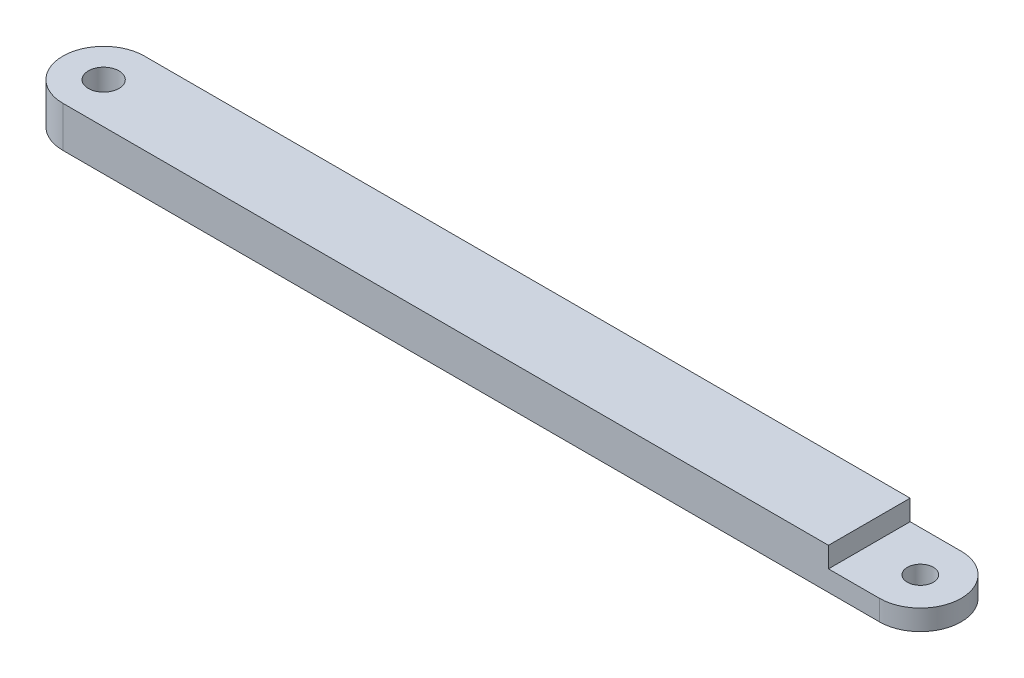
SolidWorks part; units mm, degrees
ref_plane "Front" through (0, 0, 0) normal (0, 0, 1) x (1, 0, 0)
ref_plane "Top" through (0, 0, 0) normal (0, 1, 0) x (1, 0, 0)
ref_plane "Right" through (0, 0, 0) normal (1, 0, 0) x (0, 0, -1)
sketch "Sketch1" plane through (0, 0, 0) normal (0, 1, 0) x (1, 0, 0)
  line L0 (-63.5, 0) -> (63.5, 0) construction
  line L1 (-63.5, 6.35) -> (63.5, 6.35)
  line L2 (-63.5, -6.35) -> (63.5, -6.35)
  arc A0 (-63.5, 6.35) -> (-63.5, -6.35) centre (-63.5, 0) ccw
  arc A1 (63.5, -6.35) -> (63.5, 6.35) centre (63.5, 0) ccw
  point P2 (0, 0)
  dimension "D1" = 127
  dimension "D2" = 12.7
extrude "Boss-Extrude1" add sketch "Sketch1" along normal blind 6.35
hole_wizard "3/16 (0.1875) Diameter Hole1" positions "Sketch2" profile "Sketch3" hole size "3/16" standard "ANSI Inch" end condition through all
sketch "Sketch2" plane through (0, 6.35, 0) normal (0, 1, 0) x (1, 0, 0)
  point P0 (-63.5, 0)
sketch "Sketch3" plane through (-63.5, 6.35, 0) normal (1, 0, 0) x (0, 0, 1)
  line L0 (0, 0) -> (0, 6.35)
  line L1 (0, 6.35) -> (2.3812, 6.35)
  line L2 (2.3812, 6.35) -> (2.3812, 0)
  line L5 (2.3812, 0) -> (0, 0)
  line L11 (0, -6.35) -> (0, 107.95) construction
  dimension "Thru Hole Dia." = 4.7625
  dimension "Thru Hole Depth" = 6.35
hole_wizard "#21 (0.159) Diameter Hole1" positions "Sketch5" profile "Sketch6" hole size "#21" standard "ANSI Inch" end condition through all
sketch "Sketch5" plane through (0, 6.35, 0) normal (0, 1, 0) x (1, 0, 0)
  point P0 (63.5, 0)
sketch "Sketch6" plane through (63.5, 6.35, 0) normal (1, 0, 0) x (0, 0, 1)
  line L0 (0, 0) -> (0, 6.35)
  line L1 (0, 6.35) -> (2.0193, 6.35)
  line L2 (2.0193, 6.35) -> (2.0193, 0)
  line L5 (2.0193, 0) -> (0, 0)
  line L11 (0, -6.35) -> (0, 107.95) construction
  dimension "Thru Hole Dia." = 4.0386
  dimension "Thru Hole Depth" = 6.35
sketch "Sketch4" plane through (0, 6.35, 0) normal (0, 1, 0) x (1, 0, 0)
  line L0 (63.5, 6.35) -> (-63.5, 6.35) construction
  line L1 (71.4375, -6.35) -> (55.5625, -6.35)
  line L2 (71.4375, -6.35) -> (71.4375, 6.35)
  line L3 (71.4375, 6.35) -> (55.5625, 6.35)
  line L4 (55.5625, -6.35) -> (55.5625, 6.35)
  line L5 (71.4375, -6.35) -> (55.5625, 6.35) construction
  line L6 (71.4375, 6.35) -> (55.5625, -6.35) construction
  point P0 (63.5, 0)
  dimension "D1" = 7.9375
extrude "Cut-Extrude1" cut sketch "Sketch4" against normal blind 3.175
